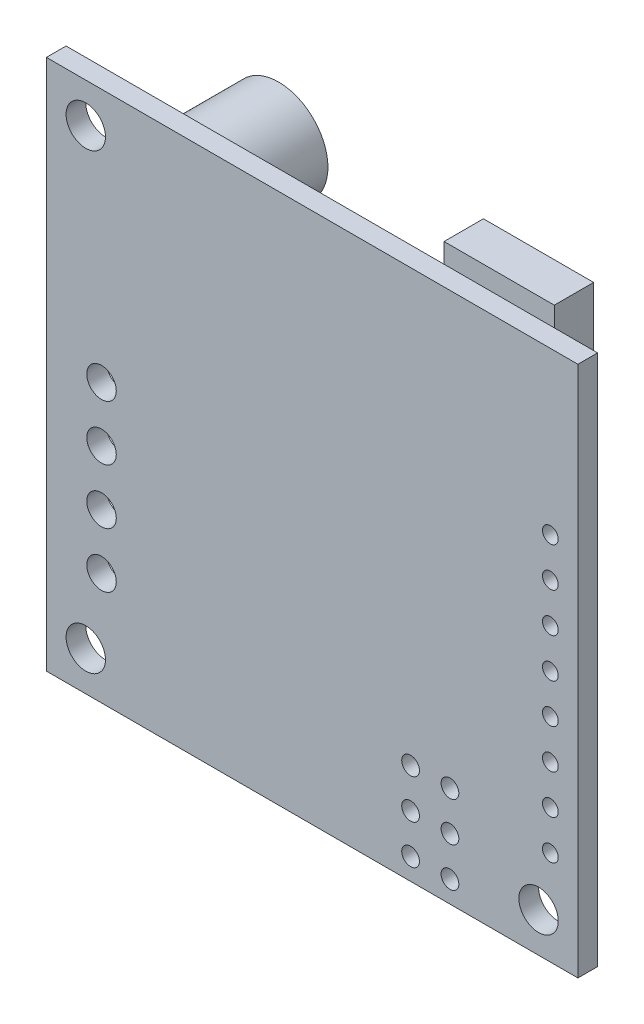
SolidWorks part; units mm, degrees
ref_plane "Front Plane" through (0, 0, 0) normal (0, 0, 1) x (1, 0, 0)
ref_plane "Top Plane" through (0, 0, 0) normal (0, 1, 0) x (1, 0, 0)
ref_plane "Right Plane" through (0, 0, 0) normal (1, 0, 0) x (0, 0, -1)
sketch "Sketch1" plane through (0, 0, 0) normal (0, 0, 1) x (1, 0, 0)
  line L1 (-17.145, -17.145) -> (17.145, -17.145)
  line L2 (-17.145, -17.145) -> (-17.145, 17.145)
  line L3 (-17.145, 17.145) -> (17.145, 17.145)
  line L4 (17.145, -17.145) -> (17.145, 17.145)
  line L5 (-17.145, -17.145) -> (17.145, 17.145) construction
  line L6 (-17.145, 17.145) -> (17.145, -17.145) construction
  point P0 (0, 0)
  dimension "D1" = 34.29
extrude "Extrude1" add sketch "Sketch1" along normal blind 1.27
sketch "Sketch2" plane through (0, 0, 1.27) normal (0, 0, 1) x (1, 0, 0)
  line L0 (-14.605, 14.605) -> (-14.605, -14.605) construction
  line L1 (-17.145, 17.145) -> (-17.145, -17.145) construction
  line L2 (-14.605, -14.605) -> (14.605, -14.605) construction
  line L3 (-17.145, -17.145) -> (17.145, -17.145) construction
  circle A0 centre (-14.605, 14.605) radius 1.27
  circle A1 centre (-14.605, -14.605) radius 1.27
  circle A2 centre (14.605, -14.605) radius 1.27
  point P6 (-17.145, 0)
  point P7 (-14.605, 0)
  point P10 (0, -14.605)
  point P11 (0, -17.145)
  dimension "D1" = 2.54
  dimension "D2" = 29.21
extrude "Extrude2" cut sketch "Sketch2" against normal through all
sketch "Sketch3" plane through (0, 0, 1.27) normal (0, 0, 1) x (1, 0, 0)
  line L0 (-17.145, -17.145) -> (17.145, -17.145) construction
  line L1 (-13.589, 0.762) -> (-13.589, -2.794) construction
  line L2 (-13.589, -2.794) -> (-13.589, -6.35) construction
  line L3 (-13.589, -6.35) -> (-13.589, -9.906) construction
  line L4 (-17.145, 17.145) -> (-17.145, -17.145) construction
  circle A0 centre (-13.589, 0.762) radius 0.9525
  circle A1 centre (-13.589, -2.794) radius 0.9525
  circle A2 centre (-13.589, -6.35) radius 0.9525
  circle A3 centre (-13.589, -9.906) radius 0.9525
  dimension "D1" = 1.905
  dimension "D2" = 7.239
  dimension "D3" = 3.556
  dimension "D4" = 3.556
extrude "Extrude3" cut sketch "Sketch3" against normal through all
sketch "Sketch4" plane through (0, 0, 1.27) normal (0, 0, 1) x (1, 0, 0)
  line L0 (-17.145, -17.145) -> (17.145, -17.145) construction
  line L1 (17.145, -17.145) -> (17.145, 17.145) construction
  circle A0 centre (6.35, -15.748) radius 0.5715
  circle A1 centre (8.89, -15.748) radius 0.5715
  dimension "D1" = 1.143
  dimension "D2" = 2.54
  dimension "D3" = 1.397
  dimension "D4" = 8.255
extrude "Extrude4" cut sketch "Sketch4" against normal through all
pattern_linear "LPattern1" count 3 spacing 2.54 along (0, 1, 0) of "Extrude4"
sketch "Sketch5" plane through (0, 0, 1.27) normal (0, 0, 1) x (1, 0, 0)
  line L0 (17.145, -17.145) -> (17.145, 17.145) construction
  line L1 (-17.145, -17.145) -> (17.145, -17.145) construction
  circle A0 centre (15.367, -11.049) radius 0.508
  dimension "D1" = 1.016
  dimension "D2" = 1.778
  dimension "D3" = 6.096
extrude "Extrude5" cut sketch "Sketch5" against normal through all
pattern_linear "LPattern2" count 8 spacing 2.54 along (0, 1, 0) of "Extrude5"
sketch "Sketch7" plane through (0, 0, 0) normal (0, 0, -1) x (-1, 0, 0)
  line L0 (-17.145, -17.145) -> (-17.145, 17.145) construction
  line L1 (-11.9056, 4.3123) -> (-4.8747, 4.3123)
  line L2 (-11.9056, 4.3123) -> (-11.9056, -0.75)
  line L3 (-11.9056, -0.75) -> (-4.8747, -0.75)
  line L4 (-4.8747, 4.3123) -> (-4.8747, -0.75)
  line L5 (1.397, -5.715) -> (9.271, -5.715)
  line L6 (1.397, -5.715) -> (1.397, -13.335)
  line L7 (1.397, -13.335) -> (9.271, -13.335)
  line L8 (9.271, -5.715) -> (9.271, -13.335)
  line L9 (0, 9.8432) -> (3.2811, 9.8432)
  line L10 (0, 9.8432) -> (0, 3.4686)
  line L11 (0, 3.4686) -> (3.2811, 3.4686)
  line L12 (3.2811, 9.8432) -> (3.2811, 3.4686)
  line L13 (4.8747, 2.2499) -> (8.2964, 2.2499)
  line L14 (4.8747, 2.2499) -> (4.8747, -2.6717)
  line L15 (4.8747, -2.6717) -> (8.2964, -2.6717)
  line L16 (8.2964, 2.2499) -> (8.2964, -2.6717)
  line L17 (-4.8747, 12.3744) -> (-2.2968, 12.3744)
  line L18 (-4.8747, 12.3744) -> (-4.8747, 10.9213)
  line L19 (-4.8747, 10.9213) -> (-2.2968, 10.9213)
  line L20 (-2.2968, 12.3744) -> (-2.2968, 10.9213)
  line L21 (0.4219, 11.9525) -> (3.5623, 11.9525)
  line L22 (0.4219, 11.9525) -> (0.4219, 10.5463)
  line L23 (0.4219, 10.5463) -> (3.5623, 10.5463)
  line L24 (3.5623, 11.9525) -> (3.5623, 10.5463)
  line L25 (-11.9056, -4.8279) -> (-8.5777, -4.8279)
  line L26 (-11.9056, -4.8279) -> (-11.9056, -5.9059)
  line L27 (-11.9056, -5.9059) -> (-8.5777, -5.9059)
  line L28 (-8.5777, -4.8279) -> (-8.5777, -5.9059)
  line L29 (-17.145, 17.145) -> (17.145, 17.145) construction
  line L30 (17.145, 17.145) -> (17.145, -17.145) construction
  line L31 (17.145, -17.145) -> (-17.145, -17.145) construction
  dimension "D1" = 7.0309
  dimension "D2" = 5.0622
  dimension "D3" = 5.2394
  dimension "D4" = 12.8327
  dimension "D5" = 1.453
  dimension "D6" = 2.578
  dimension "D7" = 12.2703
  dimension "D8" = 4.7706
  dimension "D9" = 1.4062
  dimension "D10" = 3.1405
  dimension "D11" = 5.1925
  dimension "D12" = 13.5827
  dimension "D13" = 3.2811
  dimension "D14" = 6.3747
  dimension "D15" = 7.3018
  dimension "D16" = 13.8639
  dimension "D17" = 4.9216
  dimension "D18" = 3.4217
  dimension "D19" = 14.8951
  dimension "D20" = 8.8486
  dimension "D21" = 7.62
  dimension "D22" = 7.874
  dimension "D23" = 7.874
  dimension "D24" = 3.81
extrude "Extrude7" add sketch "Sketch7" along normal blind 1.27
sketch "Sketch8" plane through (0, 0, 0) normal (0, 0, -1) x (-1, 0, 0)
  line L0 (17.145, 17.145) -> (17.145, -17.145) construction
  line L1 (-17.145, 17.145) -> (17.145, 17.145) construction
  circle A0 centre (8.509, 13.7337) radius 3.175
  circle A1 centre (12.827, 6.731) radius 3.175
  dimension "D3" = 6.35
  dimension "D1" = 4.318
  dimension "D2" = 10.414
  dimension "D4" = 3.4113
  dimension "D5" = 8.636
extrude "Extrude8" add sketch "Sketch8" along normal blind 5.08
sketch "Sketch9" plane through (0, 0, 0) normal (0, 0, -1) x (-1, 0, 0)
  line L0 (-17.145, 17.145) -> (17.145, 17.145) construction
  line L1 (-14.351, 9.525) -> (-7.239, 9.525)
  line L2 (-14.351, 9.525) -> (-14.351, 18.415)
  line L3 (-14.351, 18.415) -> (-7.239, 18.415)
  line L4 (-7.239, 9.525) -> (-7.239, 18.415)
  line L5 (-17.145, -17.145) -> (-17.145, 17.145) construction
  dimension "D1" = 7.112
  dimension "D2" = 8.89
  dimension "D3" = 7.62
  dimension "D4" = 2.794
extrude "Extrude9" add sketch "Sketch9" along normal blind 2.54
